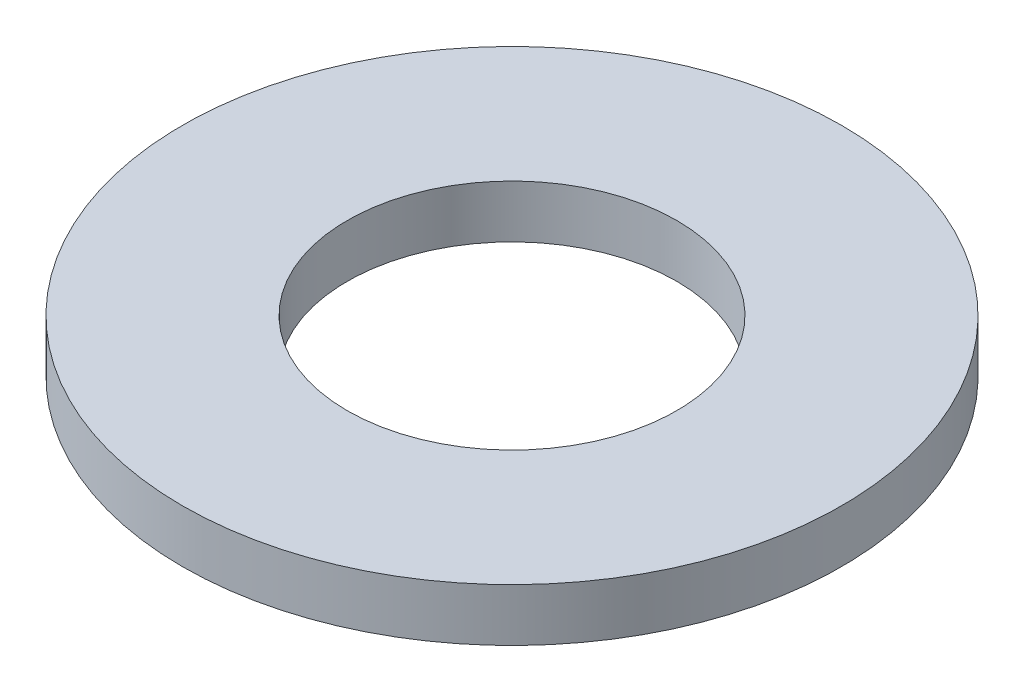
SolidWorks part; units mm, degrees
material "201 Annealed Stainless Steel (SS)"
ref_plane "Front Plane" through (0, 0, 0) normal (0, 0, 1) x (1, 0, 0)
ref_plane "Top Plane" through (0, 0, 0) normal (0, 1, 0) x (1, 0, 0)
ref_plane "Right Plane" through (0, 0, 0) normal (1, 0, 0) x (0, 0, -1)
sketch "Sketch1" plane through (0, 0, 0) normal (0, 1, 0) x (1, 0, 0)
  circle A0 centre (0, 0) radius 2.5
  circle A1 centre (0, 0) radius 5
extrude "Boss-Extrude1" add sketch "Sketch1" along normal blind 0.8
